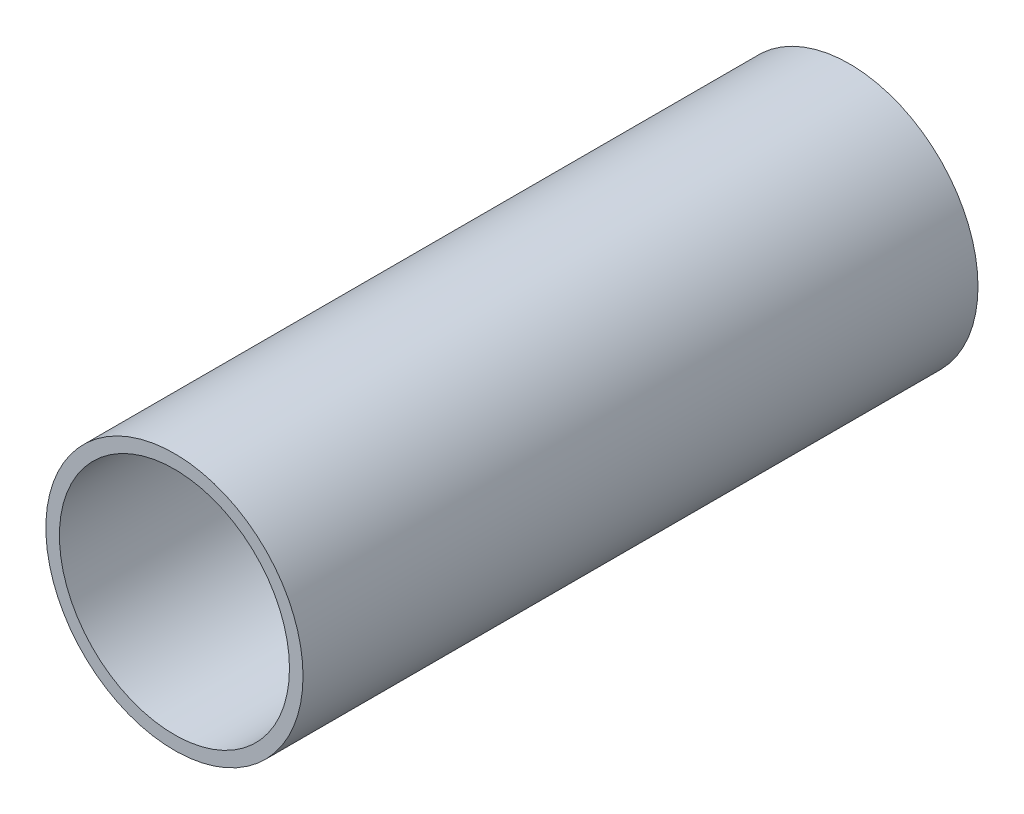
SolidWorks part; units mm, degrees
material "PVC Rigid"
ref_plane "Front Plane" through (0, 0, 0) normal (0, 0, 1) x (1, 0, 0)
ref_plane "Top Plane" through (0, 0, 0) normal (0, 1, 0) x (1, 0, 0)
ref_plane "Right Plane" through (0, 0, 0) normal (1, 0, 0) x (0, 0, -1)
sketch "Sketch1" plane through (0, 0, 0) normal (0, 0, 1) x (1, 0, 0)
  circle A0 centre (0, 0) radius 57.15
  dimension "Pipe OD" = 114.3
extrude "Extrude-Thin1" add sketch "Sketch1" along normal mid plane 300 thin thin type one direction reverse wall 6.0198
